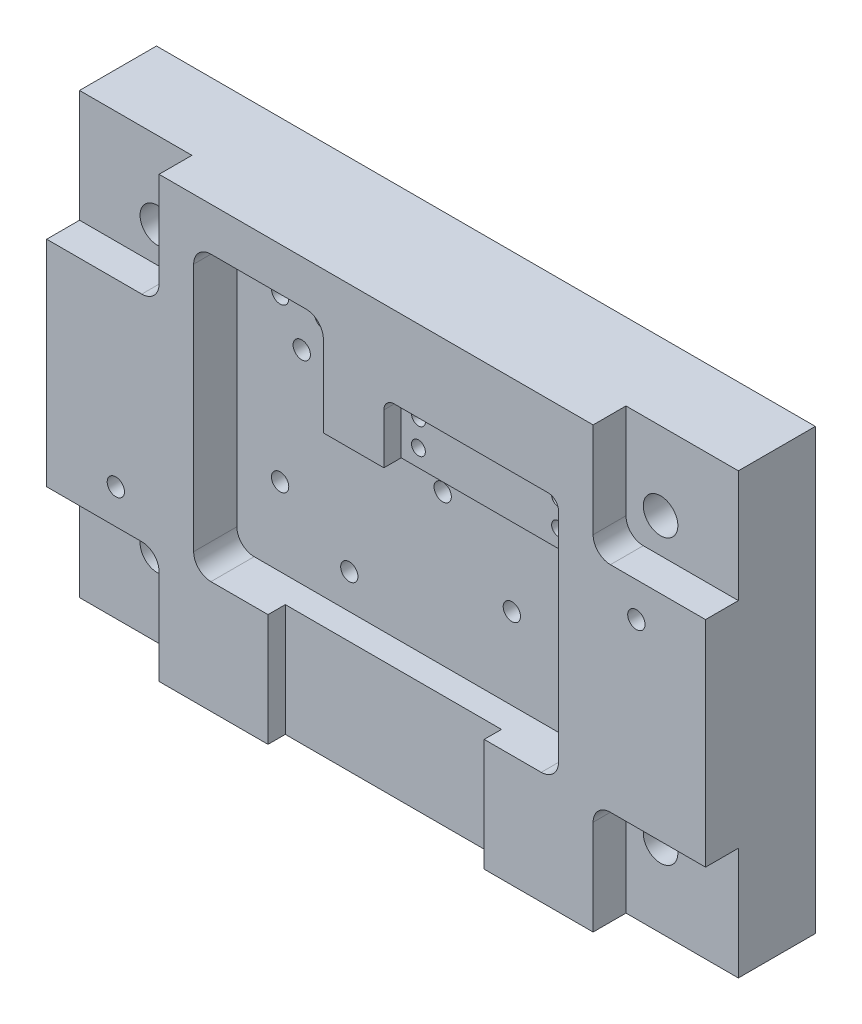
SolidWorks part; units mm, degrees
ref_plane "Alzado" through (0, 0, 0) normal (0, 0, 1) x (1, 0, 0)
ref_plane "Planta" through (0, 0, 0) normal (0, 1, 0) x (1, 0, 0)
ref_plane "Vista lateral" through (0, 0, 0) normal (1, 0, 0) x (0, 0, -1)
sketch "Croquis1" plane through (0, 0, 0) normal (0, 0, 1) x (1, 0, 0)
  line L1 (-190.5, -127) -> (190.5, -127)
  line L2 (-190.5, -127) -> (-190.5, 127)
  line L3 (-190.5, 127) -> (190.5, 127)
  line L4 (190.5, -127) -> (190.5, 127)
  line L5 (-190.5, -127) -> (190.5, 127) construction
  line L6 (-190.5, 127) -> (190.5, -127) construction
  point P0 (0, 0)
  dimension "D1" = 381
  dimension "D2" = 254
extrude "Saliente-Extruir1" add sketch "Croquis1" along normal blind 63.5
sketch "Croquis2" plane through (0, 0, 63.5) normal (0, 0, 1) x (1, 0, 0)
  line L1 (-190.5, 127) -> (-125.5, 127)
  line L2 (-190.5, 127) -> (-190.5, 62)
  line L3 (-190.5, 62) -> (-125.5, 62)
  line L4 (-125.5, 127) -> (-125.5, 62)
  line L5 (-190.5, -127) -> (-125.5, -127)
  line L6 (-190.5, -127) -> (-190.5, -62)
  line L7 (-190.5, -62) -> (-125.5, -62)
  line L8 (-125.5, -127) -> (-125.5, -62)
  line L9 (190.5, -127) -> (125.5, -127)
  line L10 (190.5, -127) -> (190.5, -62)
  line L11 (190.5, -62) -> (125.5, -62)
  line L12 (125.5, -127) -> (125.5, -62)
  line L13 (190.5, 127) -> (125.5, 127)
  line L14 (190.5, 127) -> (190.5, 62)
  line L15 (190.5, 62) -> (125.5, 62)
  line L16 (125.5, 127) -> (125.5, 62)
  dimension "D1" = 65
extrude "Cortar-Extruir1" cut sketch "Croquis2" against normal blind 19
sketch "Croquis3" plane through (0, 0, 63.5) normal (0, 0, 1) x (1, 0, 0)
  line L0 (62.5, -127) -> (62.5, -62)
  line L1 (-125.5, -127) -> (125.5, -127) construction
  line L2 (62.5, -62) -> (105.5, -62)
  line L3 (105.5, -62) -> (105.5, 80)
  line L4 (105.5, 80) -> (4.5, 80)
  line L5 (4.5, 80) -> (4.5, 45)
  line L6 (4.5, 45) -> (-30.5, 45)
  line L7 (-30.5, 45) -> (-30.5, 102)
  line L8 (-30.5, 102) -> (-105.5, 102)
  line L9 (-105.5, 102) -> (-105.5, -62)
  line L10 (-105.5, -62) -> (-62.5, -62)
  line L11 (-62.5, -62) -> (-62.5, -127)
  line L12 (-62.5, -127) -> (62.5, -127)
  line L13 (-125.5, 102) -> (-105.5, 102) construction
  line L15 (-125.5, 62) -> (-125.5, 127) construction
  line L16 (105.5, 80) -> (125.5, 80) construction
  line L17 (125.5, 127) -> (125.5, 62) construction
  line L18 (190.5, -62) -> (125.5, -62) construction
  line L19 (-125.5, -62) -> (-190.5, -62) construction
  line L20 (125.5, 62) -> (190.5, 62) construction
  line L21 (125.5, 127) -> (-125.5, 127) construction
  point P15 (108.9503, -61.7747)
  dimension "D1" = 20
  dimension "D2" = 125
  dimension "D3" = 18
  dimension "D4" = 35
  dimension "D5" = 25
  dimension "D6" = 75
extrude "Cortar-Extruir2" cut sketch "Croquis3" against normal blind 10
sketch "Croquis4" plane through (0, 0, 53.5) normal (0, 0, 1) x (1, 0, 0)
  line L12 (-62.5, -127) -> (62.5, -127)
  line L13 (62.5, -127) -> (62.5, -62)
  line L14 (62.5, -62) -> (105.5, -62)
  line L15 (105.5, -62) -> (105.5, 80)
  line L16 (105.5, 80) -> (4.5, 80)
  line L17 (4.5, 80) -> (4.5, 45)
  line L18 (4.5, 45) -> (-30.5, 45)
  line L19 (-30.5, 45) -> (-30.5, 102)
  line L20 (-30.5, 102) -> (-105.5, 102)
  line L21 (-105.5, 102) -> (-105.5, -62)
  line L22 (-105.5, -62) -> (-62.5, -62)
  line L23 (-62.5, -62) -> (-62.5, -127)
  line L27 (105.5, -62) -> (105.5, 45)
  line L30 (105.5, 45) -> (-30.5, 45)
  line L31 (-30.5, 45) -> (-30.5, 102)
  line L32 (-30.5, 102) -> (-105.5, 102)
  line L33 (-105.5, 102) -> (-105.5, -62)
  line L34 (-105.5, -62) -> (105.5, -62)
  point P2 (104.9983, 45)
  dimension "D1" = 0
extrude "Cortar-Extruir3" cut sketch "Croquis4" against normal blind 15
hole_wizard "Diámetro de taladro Ø20.0 (20)1" positions "Croquis5" profile "Croquis6" hole size "Ø20.0" standard "ISO" end condition through all
sketch "Croquis5" plane through (0, 0, 44.5) normal (0, 0, 1) x (1, 0, 0)
  line L0 (-125.5, 62) -> (-125.5, 127) construction
  line L1 (-145.5, 82) -> (-125.5, 82) construction
  line L2 (-125.5, 62) -> (-125.5, 127) construction
  line L4 (-145.5, 82) -> (-145.5, 62) construction
  line L5 (-190.5, 62) -> (-125.5, 62) construction
  line L7 (-145.5, -62) -> (-145.5, -82) construction
  line L8 (-125.5, -62) -> (-190.5, -62) construction
  line L9 (-145.5, -82) -> (-125.5, -82) construction
  line L10 (-125.5, -127) -> (-125.5, -62) construction
  line L12 (125.5, 82) -> (145.5, 82) construction
  line L13 (125.5, 127) -> (125.5, 62) construction
  line L14 (145.5, 82) -> (145.5, 62) construction
  line L15 (125.5, 62) -> (190.5, 62) construction
  line L17 (125.5, -82) -> (145.5, -82) construction
  line L18 (125.5, -62) -> (125.5, -127) construction
  line L19 (145.5, -82) -> (145.5, -62) construction
  line L20 (190.5, -62) -> (125.5, -62) construction
  point P0 (-145.5, 82)
  point P2 (-145.5, -82)
  point P4 (145.5, -82)
  point P6 (145.5, 82)
  dimension "D1" = 20
sketch "Croquis6" plane through (-145.5, 82, 44.5) normal (1, 0, 0) x (0, -1, 0)
  line L0 (0, 0) -> (0, 44.5)
  line L1 (0, 44.5) -> (10, 44.5)
  line L2 (10, 44.5) -> (10, 0)
  line L5 (10, 0) -> (0, 0)
  line L11 (0, -6.35) -> (0, 107.95) construction
  dimension "Diámetro de taladro hasta el siguiente" = 20
  dimension "Profundidad de taladro hasta el siguiente" = 44.5
hole_wizard "Diámetro de taladro Ø10.0 (10)1" positions "Croquis7" profile "Croquis8" hole size "Ø10.0" standard "ISO" end condition through all
sketch "Croquis7" plane through (0, 0, 38.5) normal (0, 0, 1) x (1, 0, 0)
  line L0 (-80.5, 77) -> (-55.5, 77) construction
  line L1 (-55.5, 77) -> (-68, 55.3494) construction
  line L2 (-68, 55.3494) -> (-80.5, 77) construction
  line L4 (-68, 77) -> (-68, 55.3494) construction
  line L6 (-68, 77) -> (-68, 102) construction
  line L7 (-30.5, 102) -> (-105.5, 102) construction
  line L9 (-105.5, 102) -> (-105.5, -62) construction
  line L10 (-105.5, -62) -> (105.5, -62) construction
  line L11 (105.5, 45) -> (4.5, 45) construction
  line L12 (13.5, 25) -> (93.5, 25) construction
  line L14 (53.5, 25) -> (53.5, -15) construction
  line L15 (105.5, -62) -> (105.5, 45) construction
  line L16 (105.5, -62) -> (105.5, 80) construction
  point P0 (-80.5, 77)
  point P2 (-55.5, 77)
  point P4 (-68, 55.3494)
  point P6 (-80.5, -17)
  point P8 (-40.5, -42)
  point P10 (13.5, 25)
  point P12 (53.5, -15)
  point P14 (93.5, 25)
  point P16 (93.5, -42)
  point P60 (96.5355, -55.9124)
  point P61 (0, 0)
  dimension "D1" = 25
  dimension "D2" = 25
  dimension "D3" = 25
  dimension "D4" = 45
  dimension "D5" = 20
  dimension "D6" = 40
  dimension "D7" = 20
  dimension "D8" = 40
  dimension "D9" = 80
  dimension "D10" = 12
  dimension "D11" = 12
sketch "Croquis8" plane through (-80.5, 77, 38.5) normal (1, 0, 0) x (0, -1, 0)
  line L0 (0, 0) -> (0, 38.5)
  line L1 (0, 38.5) -> (5, 38.5)
  line L2 (5, 38.5) -> (5, 0)
  line L5 (5, 0) -> (0, 0)
  line L11 (0, -6.35) -> (0, 107.95) construction
  dimension "Diámetro de taladro hasta el siguiente" = 10
  dimension "Profundidad de taladro hasta el siguiente" = 38.5
hole_wizard "Diámetro de taladro Ø10.0 (10)2" positions "Croquis9" profile "Croquis10" hole size "Ø10.0" standard "ISO" end condition through all
sketch "Croquis9" plane through (0, 0, 63.5) normal (0, 0, 1) x (1, 0, 0)
  line L0 (-190.5, 62) -> (-190.5, -62) construction
  line L1 (-125.5, -62) -> (-190.5, -62) construction
  line L2 (-150.5, -42) -> (-150.5, -62) construction
  line L4 (-150.5, -42) -> (-190.5, -42) construction
  line L6 (150.5, 42) -> (190.5, 42) construction
  line L7 (190.5, -62) -> (190.5, 62) construction
  line L9 (150.5, 42) -> (150.5, 62) construction
  line L10 (125.5, 62) -> (190.5, 62) construction
  point P0 (-150.5, -42)
  point P2 (150.5, 42)
  dimension "D1" = 40
  dimension "D2" = 20
sketch "Croquis10" plane through (-150.5, -42, 63.5) normal (1, 0, 0) x (0, -1, 0)
  line L0 (0, 0) -> (0, 63.5)
  line L1 (0, 63.5) -> (5, 63.5)
  line L2 (5, 63.5) -> (5, 0)
  line L5 (5, 0) -> (0, 0)
  line L11 (0, -6.35) -> (0, 107.95) construction
  dimension "Diámetro de taladro hasta el siguiente" = 10
  dimension "Profundidad de taladro hasta el siguiente" = 63.5
hole_wizard "Diámetro de taladro Ø8.0 (8)1" positions "Croquis11" profile "Croquis12" hole size "Ø8.0" standard "ISO" end condition through all
sketch "Croquis11" plane through (0, 0, 53.5) normal (0, 0, 1) x (1, 0, 0)
  line L0 (14.5, 70) -> (14.5, 55) construction
  line L1 (14.5, 55) -> (95.5, 55) construction
  line L2 (95.5, 55) -> (95.5, 70) construction
  line L3 (95.5, 70) -> (14.5, 70) construction
  line L5 (55, 70) -> (55, 80) construction
  line L6 (105.5, 80) -> (4.5, 80) construction
  line L8 (105.5, -62) -> (105.5, 80) construction
  line L9 (105.5, 45) -> (-30.5, 45) construction
  point P0 (14.5, 70)
  point P2 (95.5, 70)
  point P4 (95.5, 55)
  point P6 (14.5, 55)
  dimension "D1" = 10
  dimension "D2" = 10
  dimension "D3" = 10
sketch "Croquis12" plane through (14.5, 70, 53.5) normal (1, 0, 0) x (0, -1, 0)
  line L0 (0, 0) -> (0, 53.5)
  line L1 (0, 53.5) -> (4, 53.5)
  line L2 (4, 53.5) -> (4, 0)
  line L5 (4, 0) -> (0, 0)
  line L11 (0, -6.35) -> (0, 107.95) construction
  dimension "Diámetro de taladro hasta el siguiente" = 8
  dimension "Profundidad de taladro hasta el siguiente" = 53.5
fillet "Redondeo1" radius 10 9 edges at (105.5, 45, 46) (-30.5, 102, 51) (-105.5, 102, 51) (-105.5, -62, 51) (105.5, -62, 51) (125.5, 62, 54) (125.5, -62, 54) (-125.5, -62, 54) (-125.5, 62, 54)
fillet "Redondeo2" radius 6 2 edges at (4.5, 80, 58.5) (105.5, 80, 58.5)
